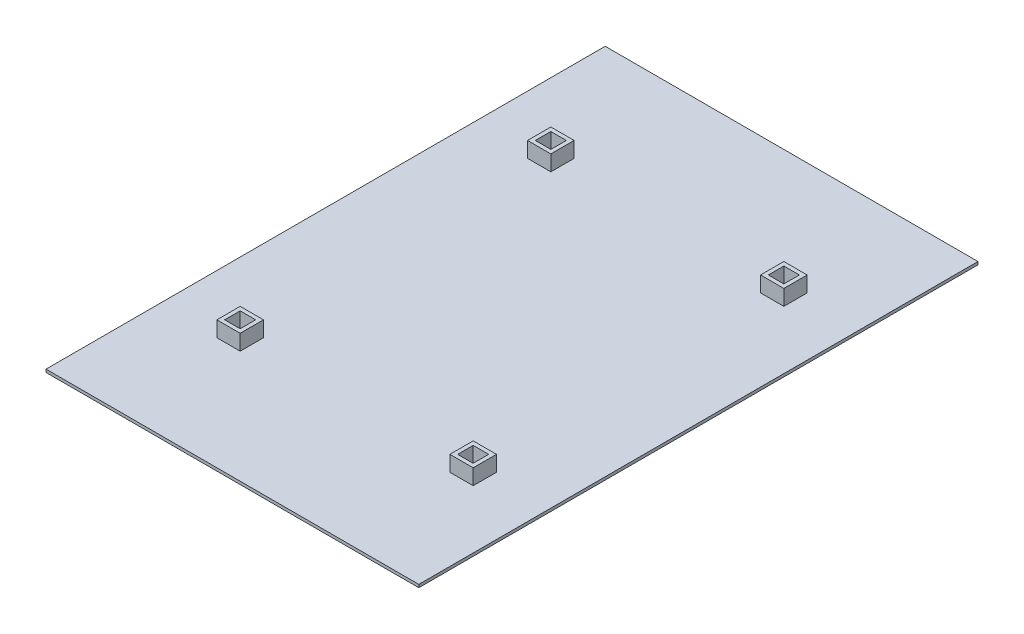
SolidWorks part; units mm, degrees
ref_plane "Front Plane" through (0, 0, 0) normal (0, 0, 1) x (1, 0, 0)
ref_plane "Top Plane" through (0, 0, 0) normal (0, 1, 0) x (1, 0, 0)
ref_plane "Right Plane" through (0, 0, 0) normal (1, 0, 0) x (0, 0, -1)
sketch "Sketch1" plane through (0, 0, 0) normal (0, 1, 0) x (1, 0, 0)
  line L1 (0, 0) -> (609.6, 0)
  line L2 (0, 0) -> (0, 914.4)
  line L3 (0, 914.4) -> (609.6, 914.4)
  line L4 (609.6, 0) -> (609.6, 914.4)
  dimension "D1" = 609.6
  dimension "D2" = 914.4
extrude "Boss-Extrude1" add sketch "Sketch1" along normal blind 4.7625
sketch "Sketch1-top plate" plane through (0, 0, 0) normal (0, 1, 0) x (1, 0, 0)
  line L1 (0, 0) -> (609.6, 0)
  line L2 (0, 0) -> (0, 914.4)
  line L3 (0, 914.4) -> (609.6, 914.4)
  line L4 (609.6, 0) -> (609.6, 914.4)
  dimension "D1" = 609.6
  dimension "D2" = 914.4
sketch "Sketch2-top plate" plane through (0, 4.7625, 0) normal (0, 1, 0) x (1, 0, 0)
  line L1 (101.6, 723.9) -> (127, 723.9)
  line L2 (101.6, 723.9) -> (101.6, 698.5)
  line L3 (101.6, 698.5) -> (127, 698.5)
  line L4 (127, 723.9) -> (127, 698.5)
  line L5 (482.6, 723.9) -> (508, 723.9)
  line L6 (482.6, 723.9) -> (482.6, 698.5)
  line L7 (482.6, 698.5) -> (508, 698.5)
  line L8 (508, 723.9) -> (508, 698.5)
  line L9 (101.6, 215.9) -> (127, 215.9)
  line L10 (101.6, 215.9) -> (101.6, 190.5)
  line L11 (101.6, 190.5) -> (127, 190.5)
  line L12 (127, 215.9) -> (127, 190.5)
  line L13 (508, 190.5) -> (482.6, 190.5)
  line L14 (508, 190.5) -> (508, 215.9)
  line L15 (508, 215.9) -> (482.6, 215.9)
  line L16 (482.6, 190.5) -> (482.6, 215.9)
  dimension "D1" = 25.4
inserted part "top plate"
sketch "Sketch4" plane through (0, 4.7625, 0) normal (0, 1, 0) x (1, 0, 0)
  line L0 (95.25, 730.25) -> (95.25, 692.15)
  line L1 (101.6, 723.9) -> (127, 723.9)
  line L2 (101.6, 723.9) -> (101.6, 698.5)
  line L3 (101.6, 698.5) -> (127, 698.5)
  line L4 (127, 723.9) -> (127, 698.5)
  line L5 (482.6, 723.9) -> (508, 723.9)
  line L6 (482.6, 723.9) -> (482.6, 698.5)
  line L7 (482.6, 698.5) -> (508, 698.5)
  line L8 (508, 723.9) -> (508, 698.5)
  line L9 (482.6, 215.9) -> (508, 215.9)
  line L10 (482.6, 215.9) -> (482.6, 190.5)
  line L11 (482.6, 190.5) -> (508, 190.5)
  line L12 (508, 215.9) -> (508, 190.5)
  line L13 (127, 190.5) -> (101.6, 190.5)
  line L14 (127, 190.5) -> (127, 215.9)
  line L15 (127, 215.9) -> (101.6, 215.9)
  line L16 (101.6, 190.5) -> (101.6, 215.9)
  line L17 (95.25, 692.15) -> (133.35, 692.15)
  line L18 (133.35, 730.25) -> (133.35, 692.15)
  line L19 (95.25, 730.25) -> (133.35, 730.25)
  line L20 (476.25, 730.25) -> (476.25, 692.15)
  line L21 (476.25, 692.15) -> (514.35, 692.15)
  line L22 (514.35, 730.25) -> (514.35, 692.15)
  line L23 (476.25, 730.25) -> (514.35, 730.25)
  line L24 (476.25, 222.25) -> (476.25, 184.15)
  line L25 (476.25, 184.15) -> (514.35, 184.15)
  line L26 (514.35, 222.25) -> (514.35, 184.15)
  line L27 (476.25, 222.25) -> (514.35, 222.25)
  line L28 (133.35, 184.15) -> (133.35, 222.25)
  line L29 (133.35, 222.25) -> (95.25, 222.25)
  line L30 (95.25, 184.15) -> (95.25, 222.25)
  line L31 (133.35, 184.15) -> (95.25, 184.15)
  dimension "D1" = 6.35
extrude "Boss-Extrude2" add sketch "Sketch4" along normal blind 25.4
